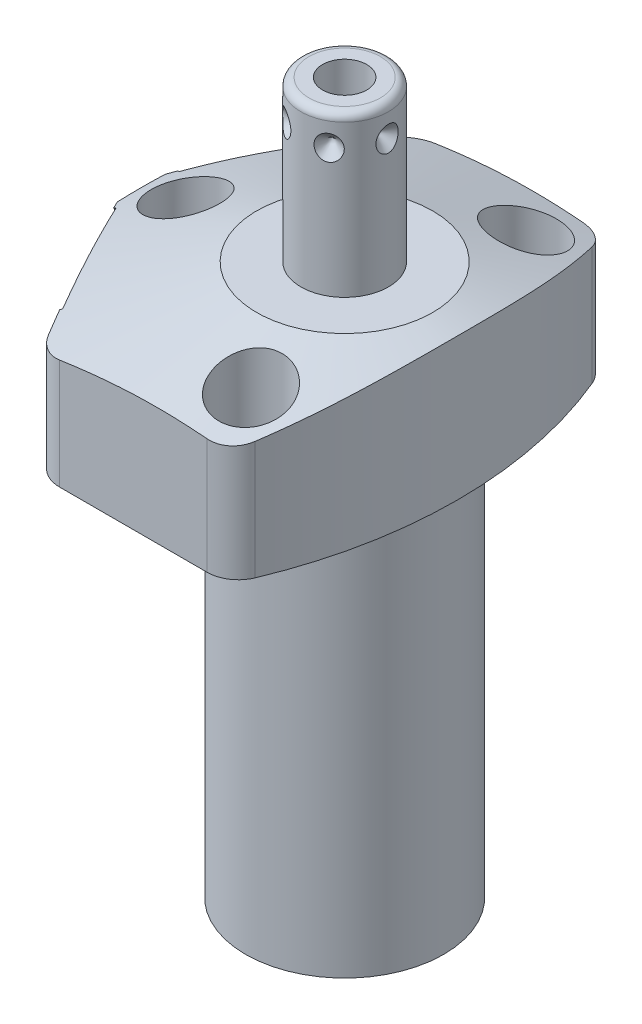
SolidWorks part; units mm, degrees
material "Alloy Steel"
ref_plane "Front Plane" through (0, 0, 0) normal (0, 0, 1) x (1, 0, 0)
ref_plane "Top Plane" through (0, 0, 0) normal (0, 1, 0) x (1, 0, 0)
ref_plane "Right Plane" through (0, 0, 0) normal (1, 0, 0) x (0, 0, -1)
ref_plane "Plane1" through (0, 0, 0) normal (0, 0, 1) x (0, -1, 0)
sketch "Sketch1" plane through (0, 0, 0) normal (0, 0, 1) x (0, -1, 0)
  line L0 (0, 28.575) -> (-19.05, 28.575)
  line L1 (-19.05, 28.575) -> (-19.05, 0)
  line L2 (-19.05, 0) -> (50.8, 0)
  line L3 (50.8, 0) -> (50.8, 12.573)
  line L4 (50.8, 12.573) -> (0, 12.573)
  line L5 (0, 12.573) -> (0, 28.575)
  line L6 (-22.5425, 0) -> (54.2925, 0) construction
  dimension "D1" = 69.85
  dimension "D2" = 19.05
  dimension "D3" = 25.146
  dimension "D4" = 57.15
revolve "Revolve1" add sketch "Sketch1" angle 360 about L6
ref_plane "Plane2" through (0, 0, 0) normal (0, -1, 0) x (0, 0, -1)
sketch "Sketch2" plane through (0, 0, 0) normal (0, -1, 0) x (0, 0, -1)
  line L0 (23.8125, -15.7954) -> (23.8125, 15.7954)
  line L2 (-23.8125, 15.7954) -> (-23.8125, -15.7954)
  line L3 (0, -18.0139) -> (0, 30.7935) construction
  arc A0 (23.8125, -15.7954) -> (23.8125, 15.7954) centre (0, 0) ccw
  circle A1 centre (0, 0) radius 28.575
  arc A2 (-23.8125, 15.7954) -> (-23.8125, -15.7954) centre (0, 0) ccw
  point P4 (0, 0)
  dimension "D1" = 47.625
  dimension "D2" = 0
extrude "Cut-Extrude1" cut sketch "Sketch2" against normal up to next
ref_plane "Plane3" through (0, 0, 0) normal (0, -1, 0) x (-1, 0, 0)
sketch "Sketch3" plane through (0, 0, 0) normal (0, -1, 0) x (-1, 0, 0)
  line L0 (14.7539, 23.8125) -> (27.4152, 0)
  line L1 (27.4152, 0) -> (14.7539, -23.8125)
  line L2 (-24.5787, -13.0687) -> (45.9515, 24.4329) construction
  line L3 (0, 0) -> (35.175, 0) construction
  line L4 (15.7954, -23.8125) -> (-15.7954, -23.8125) construction
  line L5 (-15.7954, 23.8125) -> (15.7954, 23.8125) construction
  line L6 (15.7954, -23.8125) -> (14.7539, -23.8125)
  line L7 (14.7539, 23.8125) -> (15.7954, 23.8125)
  arc A0 (15.7954, -23.8125) -> (15.7954, 23.8125) centre (0, 0) ccw construction
  arc A1 (15.7954, -23.8125) -> (15.7954, 23.8125) centre (0, 0) ccw
  dimension "D1" = 28
  dimension "D2" = 24.2062
extrude "Cut-Extrude2" cut sketch "Sketch3" against normal up to next
ref_plane "Plane4" through (0, 0, 0) normal (0, -1, 0) x (-1, 0, 0)
sketch "S2D0002" plane through (0, 0, 0) normal (0, -1, 0) x (-1, 0, 0)
  line L0 (25.8064, 53.3791) -> (25.8064, -53.3791)
  arc A0 (25.8064, 53.3791) -> (25.8064, -53.3791) centre (41.275, 0) ccw
  dimension "D1" = 55.5752
  dimension "D2" = 15.4686
  dimension "D3" = 41.275
extrude "Cut-Extrude3" cut sketch "S2D0002" against normal blind 26.035 flip side to cut
fillet "Fillet1" radius 3.9624 4 edges at (8.9402, 9.525, 23.8125) (-14.7539, 9.525, 23.8125) (-14.7539, 9.525, -23.8125) (8.9402, 9.525, -23.8125)
ref_plane "Plane5" through (0, 0, 0) normal (0, 0, 1) x (1, 0, 0)
sketch "Sketch5" plane through (0, 0, 0) normal (0, 0, 1) x (1, 0, 0)
  line L0 (-11.176, 19.05) -> (-44.45, 8.2386)
  line L1 (0, 5.9984) -> (0, 19.6715) construction
  line L2 (-15.8716, 19.05) -> (-25.8064, 19.05) construction
  line L3 (-11.176, 19.05) -> (-44.45, 19.05)
  line L4 (-44.45, 19.05) -> (-44.45, 8.2386)
  dimension "D1" = 22.352
  dimension "D2" = 18
  dimension "D3" = 44.45
revolve "Cut-Revolve1" cut sketch "Sketch5" angle 360 about L1
ref_plane "Plane6" through (-21.1485, 7.9502, -11.2449) normal (0, 1, 0) x (0.4695, 0, -0.8829)
sketch "Sketch6" plane through (-21.1485, 7.9502, -11.2449) normal (0, 1, 0) x (0.4695, 0, -0.8829)
  line L0 (0, 0) -> (4.5466, 0)
  line L1 (4.5466, 0) -> (4.1066, -2.0701)
  line L2 (4.1066, -2.0701) -> (3.4544, -2.7223)
  line L3 (3.4544, -2.7223) -> (3.4544, -12.192)
  line L4 (3.4544, -12.192) -> (0, -12.192)
  line L5 (0, -12.192) -> (0, 0)
  line L6 (0, -12.8016) -> (0, 0.6096) construction
  dimension "D1" = 12.192
revolve "Cut-Revolve2" cut sketch "Sketch6" angle 360 about L6
ref_plane "Plane7" through (-21.1485, 7.9502, 11.2449) normal (0, 1, 0) x (-0.4695, 0, -0.8829)
sketch "Sketch7" plane through (-21.1485, 7.9502, 11.2449) normal (0, 1, 0) x (-0.4695, 0, -0.8829)
  line L0 (0, 0) -> (4.5466, 0)
  line L1 (4.5466, 0) -> (4.1066, -2.0701)
  line L2 (4.1066, -2.0701) -> (3.4544, -2.7223)
  line L3 (3.4544, -2.7223) -> (3.4544, -12.192)
  line L4 (3.4544, -12.192) -> (0, -12.192)
  line L5 (0, -12.192) -> (0, 0)
  line L6 (0, -12.8016) -> (0, 0.6096) construction
  dimension "D1" = 12.192
revolve "Cut-Revolve3" cut sketch "Sketch7" angle 360 about L6
ref_plane "Plane8" through (-11.1252, 2.667, -15.875) normal (0, 0, 1) x (-1, 0, 0)
sketch "Sketch17" plane through (-21.3728, 0, 11.3641) normal (-0.8829, 0, 0.4695) x (0.4695, 0, 0.8829)
  circle A0 centre (0, 7.9502) radius 10.4775
  dimension "D1" = 20.955
extrude "Cut-Extrude4" cut sketch "Sketch17" against normal blind 0.254
sketch "Sketch18" plane through (-21.3728, 0, -11.3641) normal (-0.8829, 0, -0.4695) x (-0.4695, 0, 0.8829)
  circle A0 centre (0, 7.9502) radius 10.4775
  dimension "D1" = 20.955
extrude "Cut-Extrude5" cut sketch "Sketch18" against normal blind 0.254
sketch "Sketch8" plane through (-11.1252, 2.667, -15.875) normal (0, 0, 1) x (-1, 0, 0)
  line L0 (0, 0) -> (4.5466, 0)
  line L1 (4.5466, 0) -> (4.1066, -2.0701)
  line L2 (4.1066, -2.0701) -> (3.4544, -2.7223)
  line L3 (3.4544, -2.7223) -> (3.4544, -11.684)
  line L4 (3.4544, -11.684) -> (0, -11.684)
  line L5 (0, -11.684) -> (0, 0)
  line L6 (0, -12.2682) -> (0, 0.5842) construction
  dimension "D1" = 11.684
revolve "Cut-Revolve4" cut sketch "Sketch8" angle 360 about L6
ref_plane "Plane9" through (-11.1252, 2.667, 15.875) normal (0, 0, 1) x (-1, 0, 0)
sketch "Sketch9" plane through (-11.1252, 2.667, 15.875) normal (0, 0, 1) x (-1, 0, 0)
  line L0 (0, 0) -> (4.5466, 0)
  line L1 (4.5466, 0) -> (4.1066, -2.0701)
  line L2 (4.1066, -2.0701) -> (3.4544, -2.7223)
  line L3 (3.4544, -2.7223) -> (3.4544, -11.684)
  line L4 (3.4544, -11.684) -> (0, -11.684)
  line L5 (0, -11.684) -> (0, 0)
  line L6 (0, -12.2682) -> (0, 0.5842) construction
  dimension "D1" = 11.684
revolve "Cut-Revolve5" cut sketch "Sketch9" angle 360 about L6
ref_plane "Plane10" through (0, 0, 0) normal (1, 0, 0) x (0, 0, -1)
sketch "Sketch10" plane through (0, 0, 0) normal (1, 0, 0) x (0, 0, -1)
  line L0 (0, 19.05) -> (-5.5562, 19.05)
  line L1 (-5.5562, 19.05) -> (-5.5562, 38.3032)
  line L2 (-4.5402, 39.3192) -> (0, 39.3192)
  line L3 (0, 39.3192) -> (0, 19.05)
  line L4 (0, 18.0365) -> (0, 44.824) construction
  line L5 (11.176, 19.05) -> (-11.176, 19.05) construction
  line L6 (-21.374, 0) -> (21.374, 0) construction
  arc A0 (-4.5402, 39.3192) -> (-5.5562, 38.3032) centre (-4.5402, 38.3032) ccw
  dimension "D3" = 1.016
  dimension "D1" = 11.1125
  dimension "D2" = 39.3192
revolve "Revolve2" add sketch "Sketch10" angle 360 about L4
sketch "Sketch19" plane through (0, 0, 0) normal (0, -1, 0) x (1, 0, 0)
  circle A0 centre (-11.1252, -15.875) radius 5.5626
  circle A1 centre (-11.1252, 15.875) radius 5.5626
  dimension "D1" = 11.1252
extrude "Cut-Extrude6" cut sketch "Sketch19" against normal blind 2.667
ref_plane "Plane11" through (2.8067, 39.3192, 0) normal (0, 0, 1) x (1, 0, 0)
sketch "S2D0001" plane through (2.8067, 39.3192, 0) normal (0, 0, 1) x (1, 0, 0)
  line L0 (0, 0) -> (0, -10.16)
  line L1 (0, -10.16) -> (-2.8067, -11.8464)
  line L2 (0, 0) -> (-2.8067, 0)
  line L3 (-2.8067, 0) -> (-2.8067, -11.8464)
  line L4 (-2.8067, -17.5667) -> (-2.8067, 0.5923) construction
  line L5 (1.7335, 0) -> (-7.3469, 0) construction
  dimension "D1" = 5.6134
  dimension "D2" = 10.16
  dimension "D3" = 59
revolve "Cut-Revolve6" cut sketch "S2D0001" angle 360 about L4
ref_plane "Plane14" through (-11.1252, 0, 15.875) normal (1, 0, 0) x (0, 0, -1)
sketch "Sketch14" plane through (-11.1252, 0, 15.875) normal (1, 0, 0) x (0, 0, -1)
  line L0 (5.461, 2.667) -> (5.461, 0.9398)
  line L1 (5.461, 0.9398) -> (5.3016, 0.9398)
  line L2 (2.667, 0.4318) -> (2.667, 0.127)
  line L3 (2.667, 0.127) -> (1.5875, 0.127)
  line L4 (1.5875, 0.127) -> (1.5875, 10.6172)
  line L5 (1.5875, 10.6172) -> (3.2512, 10.6172)
  line L6 (3.2512, 10.6172) -> (3.2512, 2.667)
  line L7 (3.2512, 2.667) -> (5.461, 2.667)
  line L8 (3.175, 0.9398) -> (3.8424, 0.9398)
  line L9 (0, -1.0109) -> (0, 11.1709) construction
  line L10 (-3.4544, 14.351) -> (-3.4544, 5.3893) construction
  line L11 (3.4544, 5.3893) -> (3.4544, 14.351) construction
  line L12 (-5.499, 0) -> (37.249, 0) construction
  arc A0 (3.175, 0.9398) -> (2.667, 0.4318) centre (3.175, 0.4318) ccw
  arc A1 (3.8424, 0.9398) -> (5.3016, 0.9398) centre (4.572, 0.4318) ccw
  dimension "D5" = 0.508
  dimension "D9" = 0.889
  dimension "D1" = 2.54
  dimension "D2" = 7.9502
  dimension "D3" = 3.175
  dimension "D4" = 0.127
  dimension "D6" = 5.334
  dimension "D7" = 0.3048
  dimension "D8" = 0.3048
  dimension "D10" = 9.144
  dimension "D11" = 10.922
  dimension "D12" = 6.5024
revolve "Revolve3" add sketch "Sketch14" angle 360 about L9
ref_plane "Plane15" through (-5.5562, 35.3568, 0) normal (0, 0, 1) x (0, 1, 0)
sketch "Sketch15" plane through (-5.5562, 35.3568, 0) normal (0, 0, 1) x (0, 1, 0)
  line L0 (0, 0) -> (1.5875, 0)
  line L1 (1.5875, 0) -> (0, -1.5875)
  line L2 (0, 0) -> (0, -1.5875)
  line L3 (0, -3.7018) -> (0, 0.0794) construction
  line L4 (2.9464, 0) -> (-16.3068, 0) construction
  line L5 (3.9624, -10.0965) -> (3.9624, -1.016) construction
  dimension "D1" = 3.9624
  dimension "D2" = 3.175
  dimension "D3" = 45
ref_plane "Plane16" through (5.5562, 35.3568, 0) normal (0, 0, 1) x (0, -1, 0)
revolve "Cut-Revolve7" cut sketch "Sketch15" angle 360 about L3
pattern_circular "CirPattern1" count 6 over 360 about axis through (0, 18.0365, 0) along (0, -1, 0) of "Cut-Revolve7"
hole_wizard "Hole1" positions "Sketch21" profile "Sketch20" legacy end condition up to next
sketch "Sketch21" plane through (0, 19.05, 0) normal (0, 1, 0) x (-1, 0, 0)
  line L0 (0, 0) -> (31.1465, 0) construction
  line L1 (0, 0) -> (0, 26.4037) construction
  point P0 (-5.5626, -17.4498)
  point P9 (20.193, 0)
  point P13 (-5.5626, 17.4498)
  dimension "D1" = 5.5626
  dimension "D2" = 17.4498
  dimension "D3" = 20.193
sketch "Sketch20" plane through (5.5626, 19.05, -17.4498) normal (1, 0, 0) x (0, 0, 1)
  line L0 (0, 0) -> (0, 19.05)
  line L1 (0, 19.05) -> (2.7813, 19.05)
  line L2 (2.7813, 19.05) -> (2.7813, 11.0998)
  line L3 (2.7813, 11.0998) -> (4.3561, 11.0998)
  line L4 (4.3561, 11.0998) -> (4.3561, 0)
  line L5 (4.3561, 0) -> (0, 0)
  line L6 (0, 110) -> (0, -10) construction
  dimension "Diameter" = 5.5626
  dimension "Depth" = 19.05
  dimension "C-Bore Diameter" = 8.7122
  dimension "C-Bore Depth" = 11.0998
mirror "Mirror1" about plane through (0, 0, 0) normal (0, 0, 1) of "Revolve3"
